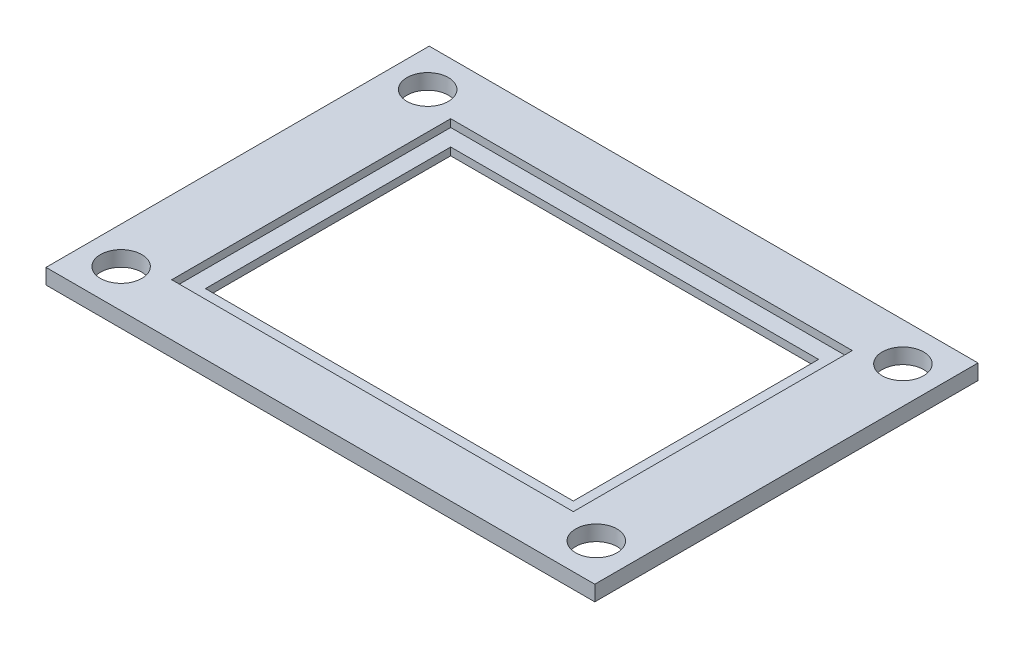
SolidWorks part; units mm, degrees
ref_plane "Front Plane" through (0, 0, 0) normal (0, 0, 1) x (1, 0, 0)
ref_plane "Top Plane" through (0, 0, 0) normal (0, 1, 0) x (1, 0, 0)
ref_plane "Right Plane" through (0, 0, 0) normal (1, 0, 0) x (0, 0, -1)
sketch "Sketch1" plane through (0, 0, 0) normal (0, 1, 0) x (1, 0, 0)
  line L1 (-17.9, -12.5) -> (17.9, -12.5)
  line L2 (-17.9, -12.5) -> (-17.9, 12.5)
  line L3 (-17.9, 12.5) -> (17.9, 12.5)
  line L4 (17.9, -12.5) -> (17.9, 12.5)
  line L5 (-17.9, -12.5) -> (17.9, 12.5) construction
  line L6 (-17.9, 12.5) -> (17.9, -12.5) construction
  line L7 (-12, -8) -> (12, -8)
  line L8 (-12, -8) -> (-12, 8)
  line L9 (-12, 8) -> (12, 8)
  line L10 (12, -8) -> (12, 8)
  line L11 (-12, -8) -> (12, 8) construction
  line L12 (-12, 8) -> (12, -8) construction
  point P0 (0, 0)
  point P6 (0, 0)
  dimension "D1" = 25
  dimension "D2" = 35.8
  dimension "D3" = 16
  dimension "D4" = 24
extrude "Boss-Extrude1" add sketch "Sketch1" along normal blind 1
sketch "Sketch2" plane through (0, 1, 0) normal (0, 1, 0) x (1, 0, 0)
  line L1 (-13.1, -9.1) -> (13.1, -9.1)
  line L2 (-13.1, -9.1) -> (-13.1, 9.1)
  line L3 (-13.1, 9.1) -> (13.1, 9.1)
  line L4 (13.1, -9.1) -> (13.1, 9.1)
  line L5 (-13.1, -9.1) -> (13.1, 9.1) construction
  line L6 (-13.1, 9.1) -> (13.1, -9.1) construction
  point P0 (0, 0)
  dimension "D1" = 18.2
  dimension "D2" = 26.2
extrude "Cut-Extrude1" cut sketch "Sketch2" against normal blind 0.5
sketch "Sketch3" plane through (0, 1, 0) normal (0, 1, 0) x (1, 0, 0)
  line L1 (-15.5, -10) -> (15.5, -10) construction
  line L2 (-15.5, -10) -> (-15.5, 10) construction
  line L3 (-15.5, 10) -> (15.5, 10) construction
  line L4 (15.5, -10) -> (15.5, 10) construction
  line L5 (-15.5, -10) -> (15.5, 10) construction
  line L6 (-15.5, 10) -> (15.5, -10) construction
  circle A0 centre (-15.5, 10) radius 1.35
  circle A1 centre (-15.5, -10) radius 1.35
  circle A2 centre (15.5, -10) radius 1.35
  circle A3 centre (15.5, 10) radius 1.35
  point P0 (0, 0)
  dimension "D1" = 2.7
  dimension "D2" = 31
  dimension "D3" = 20
extrude "Cut-Extrude2" cut sketch "Sketch3" against normal up to next
